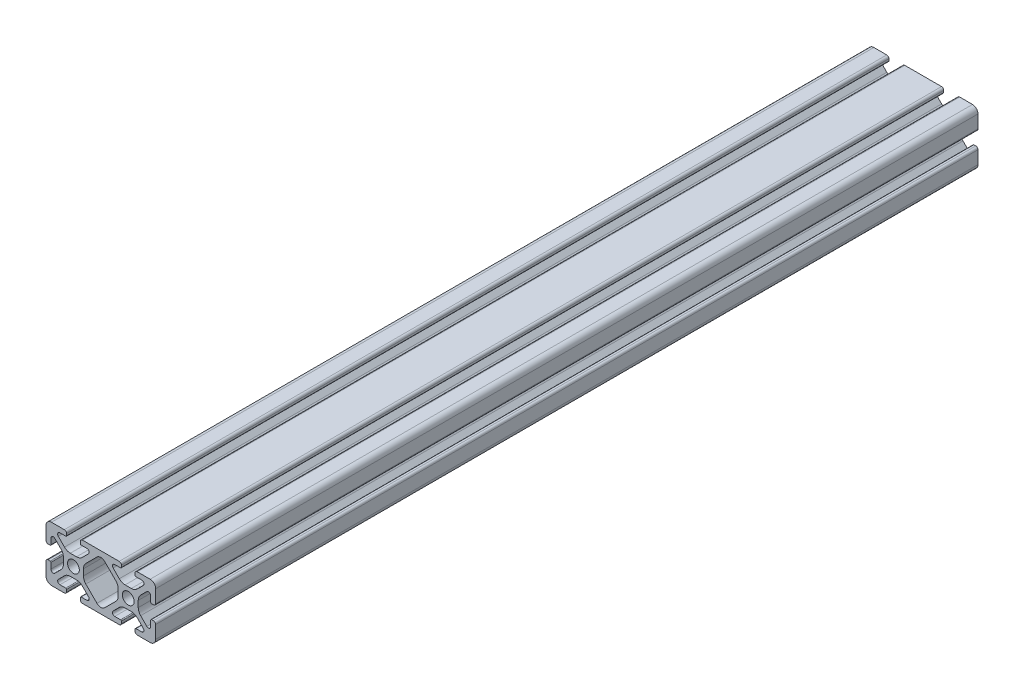
SolidWorks part; units mm, degrees
ref_plane "Ebene vorne" through (0, 0, 0) normal (0, 0, 1) x (1, 0, 0)
ref_plane "Ebene oben" through (0, 0, 0) normal (0, 1, 0) x (1, 0, 0)
ref_plane "Ebene rechts" through (0, 0, 0) normal (1, 0, 0) x (0, 0, -1)
ref_plane "Ebene1" through (0, 0, 20) normal (0, 0, 1) x (1, 0, 0)
sketch "Skizze1" plane through (0, 0, 20) normal (0, 0, 1) x (1, 0, 0)
  line L0 (18.5858, 2.687) -> (14.5287, 6.7441)
  line L1 (13.65, 8.8654) -> (13.65, 11.1346)
  line L2 (14.5287, 13.2559) -> (18.5858, 17.313)
  line L3 (21.4142, 17.313) -> (25.4713, 13.2559)
  line L4 (26.35, 11.1346) -> (26.35, 8.8654)
  line L5 (25.4713, 6.7441) -> (21.4142, 2.687)
  line L6 (32.5, 1.5) -> (32.5, 0.8)
  line L7 (33.3, 0) -> (38, 0)
  line L8 (40, 2) -> (40, 6.7)
  line L9 (39.2, 7.5) -> (38.5, 7.5)
  line L10 (38.2, 7.2) -> (38.2, 5.0824)
  line L11 (36.779, 4.4938) -> (34.5287, 6.7441)
  line L12 (33.65, 8.8654) -> (33.65, 11.1346)
  line L13 (34.5287, 13.2559) -> (36.779, 15.5062)
  line L14 (38.2, 14.9176) -> (38.2, 12.8)
  line L15 (38.5, 12.5) -> (39.2, 12.5)
  line L16 (40, 13.3) -> (40, 18)
  line L17 (38, 20) -> (33.3, 20)
  line L18 (32.5, 19.2) -> (32.5, 18.5)
  line L19 (32.8, 18.2) -> (34.9176, 18.2)
  line L20 (35.5062, 16.779) -> (33.2559, 14.5287)
  line L21 (31.1346, 13.65) -> (28.8654, 13.65)
  line L22 (26.7441, 14.5287) -> (24.4938, 16.779)
  line L23 (25.0824, 18.2) -> (27.2, 18.2)
  line L24 (27.5, 18.5) -> (27.5, 19.2)
  line L25 (26.7, 20) -> (13.3, 20)
  line L26 (12.5, 19.2) -> (12.5, 18.5)
  line L27 (12.8, 18.2) -> (14.9176, 18.2)
  line L28 (15.5062, 16.779) -> (13.2559, 14.5287)
  line L29 (11.1346, 13.65) -> (8.8654, 13.65)
  line L30 (6.7441, 14.5287) -> (4.4938, 16.779)
  line L31 (5.0824, 18.2) -> (7.2, 18.2)
  line L32 (7.5, 18.5) -> (7.5, 19.2)
  line L33 (6.7, 20) -> (2, 20)
  line L34 (0, 18) -> (0, 13.3)
  line L35 (0.8, 12.5) -> (1.5, 12.5)
  line L36 (1.8, 12.8) -> (1.8, 14.9176)
  line L37 (3.221, 15.5062) -> (5.4713, 13.2559)
  line L38 (6.35, 11.1346) -> (6.35, 8.8654)
  line L39 (5.4713, 6.7441) -> (3.221, 4.4938)
  line L40 (1.8, 5.0824) -> (1.8, 7.2)
  line L41 (1.5, 7.5) -> (0.8, 7.5)
  line L42 (0, 6.7) -> (0, 2)
  line L43 (2, 0) -> (6.7, 0)
  line L44 (7.5, 0.8) -> (7.5, 1.5)
  line L45 (7.2, 1.8) -> (5.0824, 1.8)
  line L46 (4.4938, 3.221) -> (6.7441, 5.4713)
  line L47 (8.8654, 6.35) -> (11.1346, 6.35)
  line L48 (13.2559, 5.4713) -> (15.5062, 3.221)
  line L49 (14.9176, 1.8) -> (12.8, 1.8)
  line L50 (12.5, 1.5) -> (12.5, 0.8)
  line L51 (13.3, 0) -> (26.7, 0)
  line L52 (27.5, 0.8) -> (27.5, 1.5)
  line L53 (27.2, 1.8) -> (25.0824, 1.8)
  line L54 (24.4938, 3.221) -> (26.7441, 5.4713)
  line L55 (28.8654, 6.35) -> (31.1346, 6.35)
  line L56 (33.2559, 5.4713) -> (35.5062, 3.221)
  line L57 (34.9176, 1.8) -> (32.8, 1.8)
  circle A0 centre (10, 10) radius 2.15
  circle A1 centre (30, 10) radius 2.15
  arc A2 (21.4142, 2.687) -> (18.5858, 2.687) centre (20, 4.1012) cw
  arc A3 (14.5287, 6.7441) -> (13.65, 8.8654) centre (16.65, 8.8654) cw
  arc A4 (13.65, 11.1346) -> (14.5287, 13.2559) centre (16.65, 11.1346) cw
  arc A5 (18.5858, 17.313) -> (21.4142, 17.313) centre (20, 15.8988) cw
  arc A6 (25.4713, 13.2559) -> (26.35, 11.1346) centre (23.35, 11.1346) cw
  arc A7 (26.35, 8.8654) -> (25.4713, 6.7441) centre (23.35, 8.8654) cw
  arc A8 (32.8, 1.8) -> (32.5, 1.5) centre (32.8, 1.5) ccw
  arc A9 (32.5, 0.8) -> (33.3, 0) centre (33.3, 0.8) ccw
  arc A10 (38, 0) -> (40, 2) centre (38, 2) ccw
  arc A11 (40, 6.7) -> (39.2, 7.5) centre (39.2, 6.7) ccw
  arc A12 (38.5, 7.5) -> (38.2, 7.2) centre (38.5, 7.2) ccw
  arc A13 (38.2, 5.0824) -> (36.779, 4.4938) centre (37.3676, 5.0824) cw
  arc A14 (34.5287, 6.7441) -> (33.65, 8.8654) centre (36.65, 8.8654) cw
  arc A15 (33.65, 11.1346) -> (34.5287, 13.2559) centre (36.65, 11.1346) cw
  arc A16 (36.779, 15.5062) -> (38.2, 14.9176) centre (37.3676, 14.9176) cw
  arc A17 (38.2, 12.8) -> (38.5, 12.5) centre (38.5, 12.8) ccw
  arc A18 (39.2, 12.5) -> (40, 13.3) centre (39.2, 13.3) ccw
  arc A19 (40, 18) -> (38, 20) centre (38, 18) ccw
  arc A20 (33.3, 20) -> (32.5, 19.2) centre (33.3, 19.2) ccw
  arc A21 (32.5, 18.5) -> (32.8, 18.2) centre (32.8, 18.5) ccw
  arc A22 (34.9176, 18.2) -> (35.5062, 16.779) centre (34.9176, 17.3676) cw
  arc A23 (33.2559, 14.5287) -> (31.1346, 13.65) centre (31.1346, 16.65) cw
  arc A24 (28.8654, 13.65) -> (26.7441, 14.5287) centre (28.8654, 16.65) cw
  arc A25 (24.4938, 16.779) -> (25.0824, 18.2) centre (25.0824, 17.3676) cw
  arc A26 (27.2, 18.2) -> (27.5, 18.5) centre (27.2, 18.5) ccw
  arc A27 (27.5, 19.2) -> (26.7, 20) centre (26.7, 19.2) ccw
  arc A28 (13.3, 20) -> (12.5, 19.2) centre (13.3, 19.2) ccw
  arc A29 (12.5, 18.5) -> (12.8, 18.2) centre (12.8, 18.5) ccw
  arc A30 (14.9176, 18.2) -> (15.5062, 16.779) centre (14.9176, 17.3676) cw
  arc A31 (13.2559, 14.5287) -> (11.1346, 13.65) centre (11.1346, 16.65) cw
  arc A32 (8.8654, 13.65) -> (6.7441, 14.5287) centre (8.8654, 16.65) cw
  arc A33 (4.4938, 16.779) -> (5.0824, 18.2) centre (5.0824, 17.3676) cw
  arc A34 (7.2, 18.2) -> (7.5, 18.5) centre (7.2, 18.5) ccw
  arc A35 (7.5, 19.2) -> (6.7, 20) centre (6.7, 19.2) ccw
  arc A36 (2, 20) -> (0, 18) centre (2, 18) ccw
  arc A37 (0, 13.3) -> (0.8, 12.5) centre (0.8, 13.3) ccw
  arc A38 (1.5, 12.5) -> (1.8, 12.8) centre (1.5, 12.8) ccw
  arc A39 (1.8, 14.9176) -> (3.221, 15.5062) centre (2.6324, 14.9176) cw
  arc A40 (5.4713, 13.2559) -> (6.35, 11.1346) centre (3.35, 11.1346) cw
  arc A41 (6.35, 8.8654) -> (5.4713, 6.7441) centre (3.35, 8.8654) cw
  arc A42 (3.221, 4.4938) -> (1.8, 5.0824) centre (2.6324, 5.0824) cw
  arc A43 (1.8, 7.2) -> (1.5, 7.5) centre (1.5, 7.2) ccw
  arc A44 (0.8, 7.5) -> (0, 6.7) centre (0.8, 6.7) ccw
  arc A45 (0, 2) -> (2, 0) centre (2, 2) ccw
  arc A46 (6.7, 0) -> (7.5, 0.8) centre (6.7, 0.8) ccw
  arc A47 (7.5, 1.5) -> (7.2, 1.8) centre (7.2, 1.5) ccw
  arc A48 (5.0824, 1.8) -> (4.4938, 3.221) centre (5.0824, 2.6324) cw
  arc A49 (6.7441, 5.4713) -> (8.8654, 6.35) centre (8.8654, 3.35) cw
  arc A50 (11.1346, 6.35) -> (13.2559, 5.4713) centre (11.1346, 3.35) cw
  arc A51 (15.5062, 3.221) -> (14.9176, 1.8) centre (14.9176, 2.6324) cw
  arc A52 (12.8, 1.8) -> (12.5, 1.5) centre (12.8, 1.5) ccw
  arc A53 (12.5, 0.8) -> (13.3, 0) centre (13.3, 0.8) ccw
  arc A54 (26.7, 0) -> (27.5, 0.8) centre (26.7, 0.8) ccw
  arc A55 (27.5, 1.5) -> (27.2, 1.8) centre (27.2, 1.5) ccw
  arc A56 (25.0824, 1.8) -> (24.4938, 3.221) centre (25.0824, 2.6324) cw
  arc A57 (26.7441, 5.4713) -> (28.8654, 6.35) centre (28.8654, 3.35) cw
  arc A58 (31.1346, 6.35) -> (33.2559, 5.4713) centre (31.1346, 3.35) cw
  arc A59 (35.5062, 3.221) -> (34.9176, 1.8) centre (34.9176, 2.6324) cw
extrude "Aufsatz-Linear austragen1" add sketch "Skizze1" against normal blind 300
